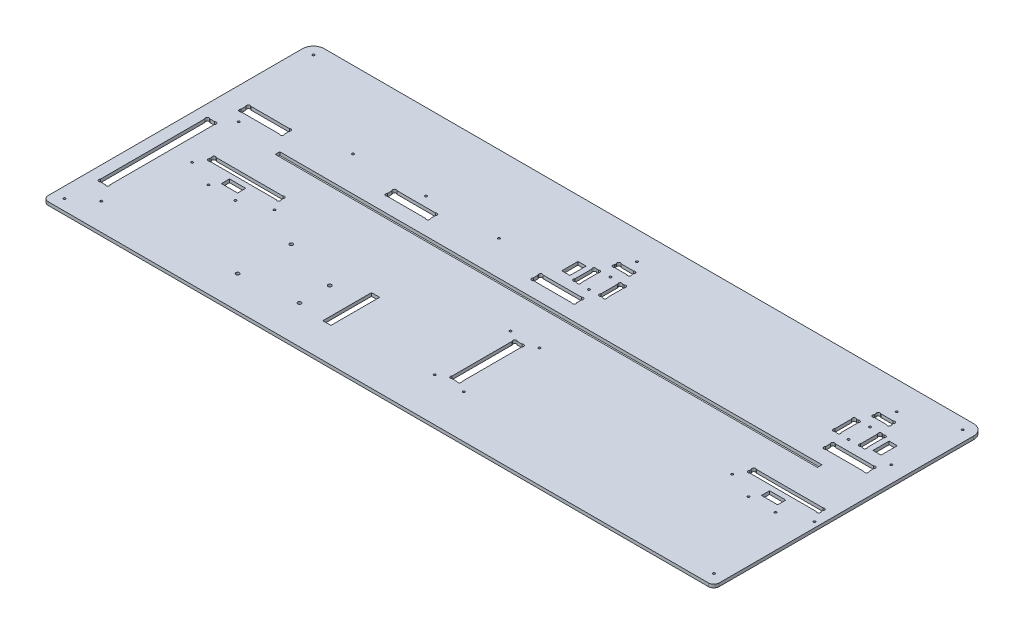
SolidWorks part; units mm, degrees
ref_plane "Plan de face" through (0, 0, 0) normal (0, 0, 1) x (1, 0, 0)
ref_plane "Plan de dessus" through (0, 0, 0) normal (0, 1, 0) x (1, 0, 0)
ref_plane "Plan de droite" through (0, 0, 0) normal (1, 0, 0) x (0, 0, -1)
sketch "Esquisse1" plane through (0, 0, 0) normal (0, 1, 0) x (1, 0, 0)
  line L26 (317, 211.2627) -> (317, 212.7373)
  line L28 (319.2627, 215) -> (330.7373, 215)
  line L29 (333, 211.2627) -> (333, 212.7373)
  line L30 (330.7373, 209) -> (319.2627, 209)
  line L31 (312.2627, 179.5) -> (313.7373, 179.5)
  line L32 (312.2627, 199.5) -> (313.7373, 199.5)
  line L33 (310, 197.2373) -> (310, 181.7627)
  line L34 (316, 181.7627) -> (316, 197.2373)
  line L35 (334, 181.7627) -> (334, 197.2373)
  line L36 (340, 197.2373) -> (340, 181.7627)
  line L37 (337.7373, 199.5) -> (336.2627, 199.5)
  line L38 (337.7373, 179.5) -> (336.2627, 179.5)
  line L39 (552.2627, 179.5) -> (553.7373, 179.5)
  line L40 (552.2627, 199.5) -> (553.7373, 199.5)
  line L41 (550, 197.2373) -> (550, 181.7627)
  line L42 (556, 181.7627) -> (556, 197.2373)
  line L43 (574, 181.7627) -> (574, 197.2373)
  line L44 (580, 197.2373) -> (580, 181.7627)
  line L45 (577.7373, 199.5) -> (576.2627, 199.5)
  line L46 (577.7373, 179.5) -> (576.2627, 179.5)
  line L47 (559.2627, 209) -> (570.7373, 209)
  line L48 (557, 211.2627) -> (557, 212.7373)
  line L49 (570.7373, 215) -> (559.2627, 215)
  line L50 (573, 211.2627) -> (573, 212.7373)
  line L55 (560, 167.7373) -> (560, 163.2627)
  line L56 (600, 167.7373) -> (600, 163.2627)
  line L57 (562.2627, 170) -> (597.7373, 170)
  line L58 (597.7373, 161) -> (562.2627, 161)
  line L59 (292.2627, 161) -> (327.7373, 161)
  line L60 (327.7373, 170) -> (292.2627, 170)
  line L61 (290, 167.7373) -> (290, 163.2627)
  line L62 (330, 167.7373) -> (330, 163.2627)
  line L64 (20, 167.7373) -> (20, 163.2627)
  line L65 (60, 167.7373) -> (60, 163.2627)
  line L66 (22.2627, 170) -> (57.7373, 170)
  line L67 (57.7373, 161) -> (22.2627, 161)
  line L70 (155, 167.7373) -> (155, 163.2627)
  line L71 (195, 167.7373) -> (195, 163.2627)
  line L72 (157.2627, 170) -> (192.7373, 170)
  line L73 (192.7373, 161) -> (157.2627, 161)
  line L76 (10, 250) -> (610, 250)
  line L77 (0, 240) -> (0, 0)
  line L78 (0, 0) -> (620, 0)
  line L79 (620, 240) -> (620, 0)
  line L84 (13.2627, 40) -> (17.7373, 40)
  line L85 (13.2627, 141) -> (17.7373, 141)
  line L86 (11, 138.7373) -> (11, 42.2627)
  line L87 (20, 42.2627) -> (20, 138.7373)
  line L98 (337.7373, 45) -> (333.2627, 45)
  line L99 (337.7373, 105) -> (333.2627, 105)
  line L100 (340, 47.2627) -> (340, 102.7373)
  line L101 (331, 102.7373) -> (331, 47.2627)
  line L109 (610, 109.2627) -> (610, 110.7373)
  line L110 (544, 109.2627) -> (544, 110.7373)
  line L111 (607.7373, 107) -> (546.2627, 107)
  line L112 (546.2627, 113) -> (607.7373, 113)
  line L113 (108.7373, 113) -> (47.2627, 113)
  line L114 (47.2627, 107) -> (108.7373, 107)
  line L115 (111, 109.2627) -> (111, 110.7373)
  line L116 (45, 109.2627) -> (45, 110.7373)
  arc A0 (319.2627, 215) -> (317, 212.7373) centre (318.1314, 213.8686) ccw
  arc A1 (319.2627, 209) -> (317, 211.2627) centre (318.1314, 210.1314) cw
  arc A2 (330.7373, 209) -> (333, 211.2627) centre (331.8686, 210.1314) ccw
  arc A3 (330.7373, 215) -> (333, 212.7373) centre (331.8686, 213.8686) cw
  arc A4 (313.7373, 179.5) -> (316, 181.7627) centre (314.8686, 180.6314) ccw
  arc A5 (312.2627, 179.5) -> (310, 181.7627) centre (311.1314, 180.6314) cw
  arc A6 (312.2627, 199.5) -> (310, 197.2373) centre (311.1314, 198.3686) ccw
  arc A7 (313.7373, 199.5) -> (316, 197.2373) centre (314.8686, 198.3686) cw
  arc A8 (336.2627, 179.5) -> (334, 181.7627) centre (335.1314, 180.6314) cw
  arc A9 (336.2627, 199.5) -> (334, 197.2373) centre (335.1314, 198.3686) ccw
  arc A10 (337.7373, 199.5) -> (340, 197.2373) centre (338.8686, 198.3686) cw
  arc A11 (337.7373, 179.5) -> (340, 181.7627) centre (338.8686, 180.6314) ccw
  arc A12 (552.2627, 179.5) -> (550, 181.7627) centre (551.1314, 180.6314) cw
  arc A13 (552.2627, 199.5) -> (550, 197.2373) centre (551.1314, 198.3686) ccw
  arc A14 (553.7373, 199.5) -> (556, 197.2373) centre (554.8686, 198.3686) cw
  arc A15 (553.7373, 179.5) -> (556, 181.7627) centre (554.8686, 180.6314) ccw
  arc A16 (576.2627, 199.5) -> (574, 197.2373) centre (575.1314, 198.3686) ccw
  arc A17 (577.7373, 199.5) -> (580, 197.2373) centre (578.8686, 198.3686) cw
  arc A18 (577.7373, 179.5) -> (580, 181.7627) centre (578.8686, 180.6314) ccw
  arc A19 (576.2627, 179.5) -> (574, 181.7627) centre (575.1314, 180.6314) cw
  arc A20 (559.2627, 215) -> (557, 212.7373) centre (558.1314, 213.8686) ccw
  arc A21 (559.2627, 209) -> (557, 211.2627) centre (558.1314, 210.1314) cw
  arc A22 (570.7373, 209) -> (573, 211.2627) centre (571.8686, 210.1314) ccw
  arc A23 (570.7373, 215) -> (573, 212.7373) centre (571.8686, 213.8686) cw
  arc A29 (560, 163.2627) -> (562.2627, 161) centre (561.1314, 162.1314) ccw
  arc A30 (560, 167.7373) -> (562.2627, 170) centre (561.1314, 168.8686) cw
  arc A31 (600, 167.7373) -> (597.7373, 170) centre (598.8686, 168.8686) ccw
  arc A32 (600, 163.2627) -> (597.7373, 161) centre (598.8686, 162.1314) cw
  arc A34 (290, 163.2627) -> (292.2627, 161) centre (291.1314, 162.1314) ccw
  arc A35 (290, 167.7373) -> (292.2627, 170) centre (291.1314, 168.8686) cw
  arc A36 (330, 167.7373) -> (327.7373, 170) centre (328.8686, 168.8686) ccw
  arc A37 (330, 163.2627) -> (327.7373, 161) centre (328.8686, 162.1314) cw
  arc A40 (20, 163.2627) -> (22.2627, 161) centre (21.1314, 162.1314) ccw
  arc A41 (20, 167.7373) -> (22.2627, 170) centre (21.1314, 168.8686) cw
  arc A42 (60, 167.7373) -> (57.7373, 170) centre (58.8686, 168.8686) ccw
  arc A43 (60, 163.2627) -> (57.7373, 161) centre (58.8686, 162.1314) cw
  arc A44 (155, 163.2627) -> (157.2627, 161) centre (156.1314, 162.1314) ccw
  arc A45 (155, 167.7373) -> (157.2627, 170) centre (156.1314, 168.8686) cw
  arc A46 (195, 163.2627) -> (192.7373, 161) centre (193.8686, 162.1314) cw
  arc A47 (195, 167.7373) -> (192.7373, 170) centre (193.8686, 168.8686) ccw
  arc A50 (17.7373, 40) -> (20, 42.2627) centre (18.8686, 41.1314) ccw
  arc A52 (13.2627, 40) -> (11, 42.2627) centre (12.1314, 41.1314) cw
  arc A53 (17.7373, 141) -> (20, 138.7373) centre (18.8686, 139.8686) cw
  arc A54 (13.2627, 141) -> (11, 138.7373) centre (12.1314, 139.8686) ccw
  arc A56 (10, 250) -> (0, 240) centre (10, 240) ccw
  arc A57 (610, 250) -> (620, 240) centre (610, 240) cw
  arc A59 (331, 47.2627) -> (333.2627, 45) centre (332.1314, 46.1314) ccw
  arc A60 (340, 47.2627) -> (337.7373, 45) centre (338.8686, 46.1314) cw
  arc A61 (331, 102.7373) -> (333.2627, 105) centre (332.1314, 103.8686) cw
  arc A62 (340, 102.7373) -> (337.7373, 105) centre (338.8686, 103.8686) ccw
  arc A64 (607.7373, 107) -> (610, 109.2627) centre (608.8686, 108.1314) ccw
  circle A65 centre (539, 98) radius 1
  arc A66 (607.7373, 113) -> (610, 110.7373) centre (608.8686, 111.8686) cw
  circle A67 centre (615, 98) radius 1
  arc A68 (546.2627, 113) -> (544, 110.7373) centre (545.1314, 111.8686) ccw
  arc A69 (546.2627, 107) -> (544, 109.2627) centre (545.1314, 108.1314) cw
  arc A70 (108.7373, 107) -> (111, 109.2627) centre (109.8686, 108.1314) ccw
  arc A71 (108.7373, 113) -> (111, 110.7373) centre (109.8686, 111.8686) cw
  arc A73 (47.2627, 113) -> (45, 110.7373) centre (46.1314, 111.8686) ccw
  arc A75 (47.2627, 107) -> (45, 109.2627) centre (46.1314, 108.1314) cw
  point P1 (337, 199.5)
  point P7 (340, 189.5)
  dimension "D25" = 6
  dimension "D28" = 16
  dimension "D29" = 20
  dimension "D32" = 9.5
  dimension "D33" = 35
  dimension "D39" = 10
  dimension "D49" = 1.1314
  dimension "D57" = 6
  dimension "D55" = 10
  dimension "D62" = 5
  dimension "D63" = 1.6
  dimension "D64" = 9
  dimension "D65" = 1.1314
  dimension "D66" = 1.1314
  dimension "D67" = 620
  dimension "D9" = 2.2627
  dimension "D10" = 1.6
  dimension "D78" = 3.7373
  dimension "D14" = 1.6
  dimension "D36" = 1.6
  dimension "D61" = 1.6
  dimension "D95" = 1.6
  dimension "D107" = 1.6
  dimension "D118" = 1.6
  dimension "D119" = 1.6
  dimension "D128" = 6
  dimension "D141" = 1.6
  dimension "D58" = 2
  dimension "D2" = 250
  dimension "D8" = 20
  dimension "D13" = 40
  dimension "D16" = 1.1314
  dimension "D17" = 1.1314
  dimension "D19" = 2.2627
  dimension "D20" = 2.2627
  dimension "D21" = 80
  dimension "D22" = 9
  dimension "D23" = 1.1314
  dimension "D24" = 1.1314
  dimension "D26" = 6
  dimension "D27" = 6
  dimension "D30" = 40
  dimension "D31" = 18
  dimension "D37" = 1.1314
  dimension "D38" = 2.2627
  dimension "D40" = 1.1314
  dimension "D41" = 1.1314
  dimension "D42" = 1.1314
  dimension "D43" = 1.1314
  dimension "D45" = 1
  dimension "D46" = 1.1314
  dimension "D47" = 1.1314
  dimension "D48" = 1.1314
  dimension "D51" = 3.7373
  dimension "D52" = 66
  dimension "D53" = 10
  dimension "D54" = 66
  dimension "D56" = 107
  dimension "D59" = 1.1314
  dimension "D60" = 2.2627
  dimension "D68" = 60
  dimension "D70" = 6
  dimension "D72" = 1.1314
  dimension "D73" = 1.1314
  dimension "D74" = 63.7373
  dimension "D75" = 2.2627
  dimension "D76" = 2.2627
  dimension "D77" = 45
  dimension "D79" = 45
  dimension "D83" = 280
  dimension "D84" = 1.1314
  dimension "D85" = 1.1314
  dimension "D86" = 1.1314
  dimension "D87" = 1.1314
  dimension "D88" = 9
  dimension "D89" = 101
  dimension "D90" = 40
  dimension "D91" = 11
  dimension "D96" = 1.1314
  dimension "D97" = 1.1314
  dimension "D98" = 1.1314
  dimension "D100" = 1.1314
  dimension "D105" = 9
  dimension "D106" = 40
  dimension "D108" = 20
  dimension "D109" = 80
  dimension "D110" = 1.1314
  dimension "D111" = 1.1314
  dimension "D112" = 1.1314
  dimension "D113" = 1.1314
  dimension "D114" = 40
  dimension "D115" = 95
  dimension "D116" = 95
  dimension "D117" = 40
  dimension "D120" = 1.1314
  dimension "D121" = 1.1314
  dimension "D122" = 1.1314
  dimension "D123" = 1.1314
  dimension "D124" = 1.1314
  dimension "D125" = 1.1314
  dimension "D126" = 1.1314
  dimension "D127" = 1.1314
  dimension "D129" = 6
  dimension "D130" = 6
  dimension "D132" = 20
  dimension "D133" = 16
  dimension "D135" = 35
  dimension "D136" = 9.5
  dimension "D139" = 1
  dimension "D140" = 18
  dimension "D142" = 1.1314
  dimension "D143" = 1.1314
  dimension "D144" = 1.1314
  dimension "D145" = 1.1314
  dimension "D146" = 1.1314
  dimension "D147" = 1.1314
  dimension "D148" = 1.1314
  dimension "D149" = 1.1314
  dimension "D150" = 1.1314
  dimension "D151" = 1.1314
  dimension "D152" = 1.1314
  dimension "D153" = 1.1314
  dimension "D154" = 9
  dimension "D155" = 5
extrude "Extrusion1" add sketch "Esquisse1" along normal blind 3
sketch "Esquisse2" plane through (0, 3, 0) normal (0, 1, 0) x (-1, 0, 0)
  line L0 (-610, -250) -> (-10, -250) construction
  line L5 (-620, 21.4973) -> (-620, -261.3021) construction
  line L7 (-573, -142.8) -> (-72, -142.8)
  line L8 (-573, -142.8) -> (-573, -147)
  line L9 (-573, -147) -> (-72, -147)
  line L10 (-72, -142.8) -> (-72, -147)
  dimension "D1" = 47
  dimension "D2" = 4.2
  dimension "D3" = 501
  dimension "D4" = 103
extrude "Enlèv. mat.-Extru.1" cut sketch "Esquisse2" against normal through all
sketch "Esquisse3" plane through (0, 3, 0) normal (0, 1, 0) x (1, 0, 0)
  line L0 (574, 197.2373) -> (574, 181.7627) construction
  line L1 (556, 181.7627) -> (556, 197.2373) construction
  line L2 (559.2627, 209) -> (570.7373, 209) construction
  line L4 (576.2627, 179.5) -> (577.7373, 179.5) construction
  line L5 (577.7373, 199.5) -> (576.2627, 199.5) construction
  line L6 (334, 197.2373) -> (334, 181.7627) construction
  circle A0 centre (565, 179.5) radius 1
  circle A1 centre (565, 199.5) radius 1
  circle A2 centre (325, 179.5) radius 1
  circle A3 centre (325, 199.5) radius 1
  dimension "D1" = 2
  dimension "D2" = 9
  dimension "D3" = 9
  dimension "D4" = 20
  dimension "D5" = 9.5
  dimension "D6" = 0
  dimension "D7" = 0
  dimension "D8" = 9
extrude "Enlèv. mat.-Extru.2" cut sketch "Esquisse3" against normal through all
fillet "Congé1" radius 5 2 edges at (620, 1.5, 0) (0, 1.5, 0)
sketch "Esquisse4" plane through (0, 0, 0) normal (0, -1, 0) x (1, 0, 0)
  line L0 (0, -240) -> (0, -5) construction
  line L1 (5, 0) -> (615, 0) construction
  line L2 (610, -250) -> (10, -250) construction
  line L3 (620, -5) -> (620, -240) construction
  circle A0 centre (10, -10) radius 1
  circle A1 centre (610, -10) radius 1
  circle A2 centre (610, -240) radius 1
  circle A3 centre (10, -240) radius 1
  dimension "D1" = 2
  dimension "D2" = 10
  dimension "D3" = 10
  dimension "D4" = 10
  dimension "D5" = 10
  dimension "D6" = 10
  dimension "D7" = 10
  dimension "D8" = 10
  dimension "D9" = 10
extrude "Enlèv. mat.-Extru.3" cut sketch "Esquisse4" against normal through all
sketch "Esquisse5" plane through (0, 3, 0) normal (0, 1, 0) x (1, 0, 0)
  line L1 (0, 240) -> (0, 5) construction
  line L2 (5, 0) -> (615, 0) construction
  circle A0 centre (151.27, 78.26) radius 1.59
  circle A1 centre (150, 30) radius 1.59
  circle A2 centre (202.07, 63.02) radius 1.59
  circle A3 centre (202.07, 35.08) radius 1.59
  dimension "D1" = 3.18
  dimension "D7" = 30
  dimension "D2" = 48.26
  dimension "D3" = 27.94
  dimension "D4" = 52.07
  dimension "D5" = 5.08
  dimension "D6" = 150
  dimension "D8" = 1.27
extrude "Enlèv. mat.-Extru.4" cut sketch "Esquisse5" against normal through all
sketch "Esquisse6" plane through (0, 3, 0) normal (0, 1, 0) x (1, 0, 0)
  line L0 (544, 110.7373) -> (544, 109.2627) construction
  line L1 (569.5, 102) -> (584.5, 102)
  line L2 (569.5, 102) -> (569.5, 94.5)
  line L3 (569.5, 94.5) -> (584.5, 94.5)
  line L4 (584.5, 102) -> (584.5, 94.5)
  line L5 (610, 109.2627) -> (610, 110.7373) construction
  line L6 (546.2627, 107) -> (607.7373, 107) construction
  line L8 (585, 197) -> (592.5, 197)
  line L9 (585, 197) -> (585, 182)
  line L10 (585, 182) -> (592.5, 182)
  line L11 (592.5, 197) -> (592.5, 182)
  line L12 (305, 197) -> (297.5, 197)
  line L13 (305, 197) -> (305, 182)
  line L14 (305, 182) -> (297.5, 182)
  line L15 (297.5, 197) -> (297.5, 182)
  line L16 (577.7373, 199.5) -> (576.2627, 199.5) construction
  line L17 (576.2627, 179.5) -> (577.7373, 179.5) construction
  line L18 (580, 181.7627) -> (580, 197.2373) construction
  line L19 (310, 197.2373) -> (310, 181.7627) construction
  line L20 (313.7373, 199.5) -> (312.2627, 199.5) construction
  line L21 (45, 110.7373) -> (45, 109.2627) construction
  line L22 (227.07, 76.63) -> (234.57, 76.63)
  line L23 (227.07, 76.63) -> (227.07, 31.63)
  line L24 (227.07, 31.63) -> (234.57, 31.63)
  line L25 (234.57, 76.63) -> (234.57, 31.63)
  line L26 (70.5, 102) -> (85.5, 102)
  line L27 (70.5, 102) -> (70.5, 94.5)
  line L28 (70.5, 94.5) -> (85.5, 94.5)
  line L29 (85.5, 102) -> (85.5, 94.5)
  circle A0 centre (150, 30) radius 1.59 construction
  circle A1 centre (151.27, 78.26) radius 1.59 construction
  circle A2 centre (202.07, 63.02) radius 1.59 construction
  dimension "D1" = 15
  dimension "D2" = 7.5
  dimension "D3" = 25.5
  dimension "D4" = 25.5
  dimension "D5" = 5
  dimension "D6" = 7.5
  dimension "D7" = 15
  dimension "D8" = 15
  dimension "D9" = 7.5
  dimension "D10" = 2.5
  dimension "D11" = 2.5
  dimension "D12" = 5
  dimension "D13" = 5
  dimension "D14" = 2.5
  dimension "D15" = 7.5
  dimension "D16" = 45
  dimension "D17" = 1.63
  dimension "D18" = 1.63
  dimension "D19" = 25
  dimension "D20" = 15
  dimension "D21" = 25.5
extrude "Enlèv. mat.-Extru.5" cut sketch "Esquisse6" against normal through all
sketch "Esquisse7" plane through (0, 3, 0) normal (0, 1, 0) x (1, 0, 0)
  line L0 (70.5, 102) -> (70.5, 94.5) construction
  line L1 (85.5, 94.5) -> (85.5, 102) construction
  line L2 (70.5, 94.5) -> (85.5, 94.5) construction
  line L3 (569.5, 94.5) -> (584.5, 94.5) construction
  line L4 (584.5, 94.5) -> (584.5, 102) construction
  line L5 (569.5, 102) -> (569.5, 94.5) construction
  line L6 (47.2627, 107) -> (108.7373, 107) construction
  line L7 (45, 110.7373) -> (45, 109.2627) construction
  line L8 (111, 109.2627) -> (111, 110.7373) construction
  circle A0 centre (589.5, 87.5) radius 1
  circle A1 centre (564.5, 87.5) radius 1
  circle A6 centre (65.5, 87.5) radius 1
  circle A7 centre (90.5, 87.5) radius 1
  circle A8 centre (116, 98) radius 1
  circle A9 centre (40, 98) radius 1
  dimension "D1" = 2
  dimension "D8" = 2
  dimension "D2" = 5
  dimension "D3" = 5
  dimension "D4" = 7
  dimension "D5" = 7
  dimension "D6" = 5
  dimension "D7" = 5
  dimension "D10" = 5
  dimension "D11" = 9
  dimension "D12" = 5
extrude "Enlèv. mat.-Extru.6" cut sketch "Esquisse7" against normal through all
sketch "Esquisse8" plane through (0, 3, 0) normal (0, 1, 0) x (1, 0, 0)
  line L0 (5, 0) -> (615, 0) construction
  line L1 (0, 240) -> (0, 5) construction
  line L2 (330.7373, 215) -> (319.2627, 215) construction
  line L3 (570.7373, 215) -> (559.2627, 215) construction
  line L4 (597.7373, 170) -> (562.2627, 170) construction
  line L5 (331, 102.7373) -> (331, 47.2627) construction
  line L6 (340, 47.2627) -> (340, 102.7373) construction
  line L7 (192.7373, 170) -> (157.2627, 170) construction
  circle A0 centre (29, 25) radius 1
  circle A1 centre (29, 152) radius 1
  circle A2 centre (107.5, 179) radius 1
  circle A3 centre (242.5, 179) radius 1
  circle A4 centre (175, 179) radius 1
  circle A5 centre (325, 224) radius 1
  circle A6 centre (565, 224) radius 1
  circle A7 centre (605, 179) radius 1
  circle A9 centre (322, 40) radius 1
  circle A10 centre (322, 110) radius 1
  circle A11 centre (349, 110) radius 1
  circle A12 centre (349, 40) radius 1
  point P22 (565, 215)
  point P24 (325, 215)
  point P38 (0, 0)
  point P49 (175, 170)
  dimension "D1" = 2
  dimension "D4" = 127
  dimension "D5" = 67.5
  dimension "D13" = 9
  dimension "D2" = 25
  dimension "D3" = 29
  dimension "D7" = 9
  dimension "D8" = 67.5
  dimension "D9" = 9
  dimension "D10" = 40
  dimension "D11" = 9
  dimension "D12" = 40
  dimension "D14" = 9
  dimension "D15" = 70
extrude "Enlèv. mat.-Extru.7" cut sketch "Esquisse8" against normal through all
